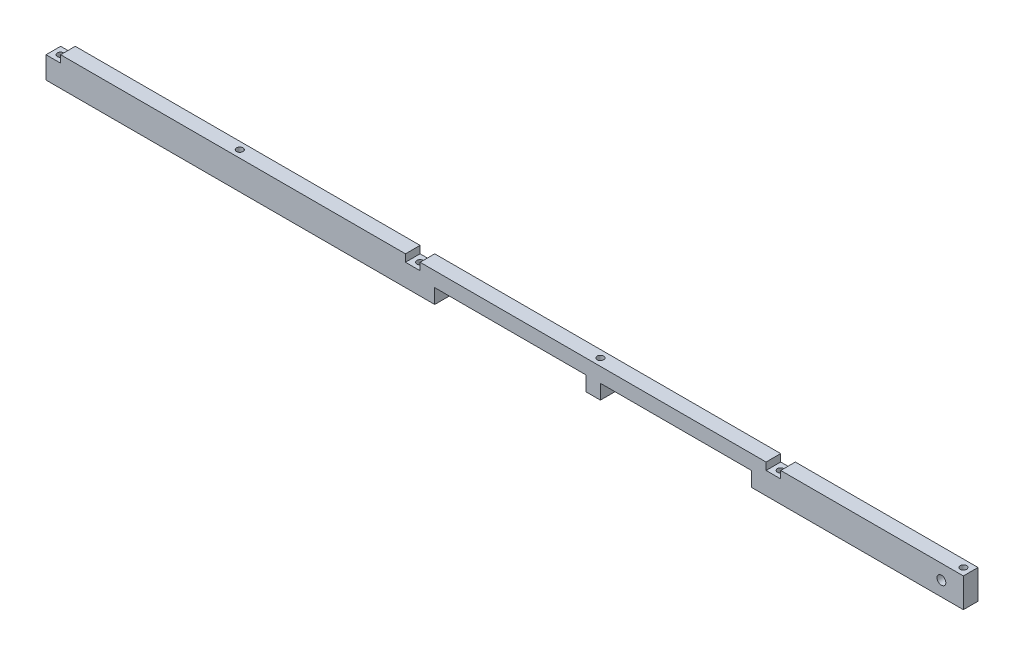
SolidWorks part; units mm, degrees
ref_plane "Front Plane" through (0, 0, 0) normal (0, 0, 1) x (1, 0, 0)
ref_plane "Top Plane" through (0, 0, 0) normal (0, 1, 0) x (1, 0, 0)
ref_plane "Right Plane" through (0, 0, 0) normal (1, 0, 0) x (0, 0, -1)
sketch "Sketch1" plane through (0, 0, 0) normal (1, 0, 0) x (0, 0, -1)
  line L1 (0, 0) -> (6.35, 0)
  line L2 (0, 0) -> (0, 12.7)
  line L3 (0, 12.7) -> (6.35, 12.7)
  line L4 (6.35, 0) -> (6.35, 12.7)
  dimension "D1" = 6.35
  dimension "D2" = 12.7
extrude "Boss-Extrude1" add sketch "Sketch1" along normal blind 398.018
hole_wizard "#34 (0.111) Diameter Hole1" positions "Sketch4" profile "Sketch5" hole size "#34" standard "ANSI Inch" end condition through all
sketch "Sketch4" plane through (0, 12.7, 0) normal (0, 1, 0) x (1, 0, 0)
  line L0 (0, 3.175) -> (398.018, 3.175) construction
  line L1 (0, 6.35) -> (0, 0) construction
  line L2 (398.018, 6.35) -> (398.018, 0) construction
  point P9 (3.175, 3.175)
  point P11 (159.131, 3.175)
  point P13 (80.899, 3.175)
  point P15 (237.363, 3.175)
  point P17 (315.595, 3.175)
  point P19 (394.843, 3.175)
  dimension "D1" = 3.175
  dimension "D2" = 77.724
  dimension "D3" = 78.232
  dimension "D4" = 78.232
  dimension "D5" = 78.232
  dimension "D6" = 79.248
sketch "Sketch5" plane through (3.175, 12.7, -3.175) normal (1, 0, 0) x (0, 0, 1)
  line L0 (0, 0) -> (0, 12.7)
  line L1 (0, 12.7) -> (1.4097, 12.7)
  line L2 (1.4097, 12.7) -> (1.4097, 0)
  line L5 (1.4097, 0) -> (0, 0)
  line L11 (0, -6.35) -> (0, 107.95) construction
  dimension "Thru Hole Dia." = 2.8194
  dimension "Thru Hole Depth" = 12.7
sketch "Sketch6" plane through (0, 0, 0) normal (0, 0, 1) x (1, 0, 0)
  line L0 (1.7653, 6.35) -> (4.5847, 6.35) construction
  line L1 (1.7653, 12.7) -> (1.7653, 0) construction
  line L2 (4.5847, 0) -> (4.5847, 12.7) construction
  line L3 (4.5847, 6.35) -> (79.4893, 6.35) construction
  line L4 (79.4893, 12.7) -> (79.4893, 0) construction
  line L6 (82.3087, 0) -> (82.3087, 12.7) construction
  line L7 (82.3087, 6.35) -> (157.7213, 6.35) construction
  line L8 (157.7213, 12.7) -> (157.7213, 0) construction
  line L9 (157.7213, 6.35) -> (160.5407, 6.35) construction
  line L10 (160.5407, 0) -> (160.5407, 12.7) construction
  line L11 (160.5407, 6.35) -> (235.9533, 6.35) construction
  line L12 (235.9533, 12.7) -> (235.9533, 0) construction
  line L14 (238.7727, 0) -> (238.7727, 12.7) construction
  line L15 (238.7727, 6.35) -> (314.1853, 6.35) construction
  line L16 (314.1853, 12.7) -> (314.1853, 0) construction
  line L17 (314.1853, 6.35) -> (317.0047, 6.35) construction
  line L18 (317.0047, 0) -> (317.0047, 12.7) construction
  line L19 (317.0047, 6.35) -> (393.4333, 6.35) construction
  line L20 (393.4333, 12.7) -> (393.4333, 0) construction
  line L23 (3.175, 6.35) -> (3.175, 12.7) construction
  line L24 (398.018, 12.7) -> (0, 12.7) construction
  line L26 (80.899, 12.7) -> (159.131, 6.35) construction
  line L27 (159.131, 6.35) -> (159.131, 12.7) construction
  line L28 (159.131, 12.7) -> (237.363, 6.35) construction
  line L30 (237.363, 12.7) -> (315.595, 6.35) construction
  line L31 (315.595, 6.35) -> (315.595, 12.7) construction
  line L32 (315.595, 12.7) -> (394.843, 6.35) construction
  line L41 (312.42, 9.525) -> (318.77, 9.525)
  line L42 (312.42, 9.525) -> (312.42, 15.875)
  line L43 (312.42, 15.875) -> (318.77, 15.875)
  line L44 (318.77, 9.525) -> (318.77, 15.875)
  line L45 (312.42, 9.525) -> (318.77, 15.875) construction
  line L46 (312.42, 15.875) -> (318.77, 9.525) construction
  line L53 (155.956, 9.525) -> (162.306, 9.525)
  line L54 (155.956, 9.525) -> (155.956, 15.875)
  line L55 (155.956, 15.875) -> (162.306, 15.875)
  line L56 (162.306, 9.525) -> (162.306, 15.875)
  line L57 (155.956, 9.525) -> (162.306, 15.875) construction
  line L58 (155.956, 15.875) -> (162.306, 9.525) construction
  line L65 (0, 9.525) -> (6.35, 9.525)
  line L66 (0, 9.525) -> (0, 15.875)
  line L67 (0, 15.875) -> (6.35, 15.875)
  line L68 (6.35, 9.525) -> (6.35, 15.875)
  line L69 (0, 9.525) -> (6.35, 15.875) construction
  line L70 (0, 15.875) -> (6.35, 9.525) construction
  dimension "D1" = 6.35
  dimension "D3" = 6.35
  dimension "D5" = 6.35
  dimension "D7" = 6.35
  dimension "D9" = 6.35
  dimension "D10" = 6.35
extrude "Cut-Extrude1" cut sketch "Sketch6" against normal through all
hole_wizard "Tap Drill for #10-24 Tap1" positions "Sketch8" profile "Sketch7" hole size "#10-24" standard "ANSI Inch" end condition through all
sketch "Sketch8" plane through (0, 0, 0) normal (0, 0, 1) x (1, 0, 0)
  line L0 (398.018, 6.35) -> (388.493, 6.35) construction
  line L1 (398.018, 12.7) -> (398.018, 0) construction
  point P2 (388.493, 6.35)
sketch "Sketch7" plane through (388.493, 6.35, 0) normal (1, 0, 0) x (0, -1, 0)
  line L0 (0, 0) -> (0, 6.35)
  line L1 (0, 6.35) -> (1.8986, 6.35)
  line L2 (1.8986, 6.35) -> (1.8986, 0)
  line L5 (1.8986, 0) -> (0, 0)
  line L11 (0, -6.35) -> (0, 107.95) construction
  dimension "Thru Hole Dia." = 3.7973
  dimension "Thru Hole Depth" = 6.35
sketch "Sketch9" plane through (0, 0, 0) normal (0, 0, 1) x (1, 0, 0)
  line L0 (398.018, 0) -> (0, 0) construction
  line L1 (306.07, 0) -> (240.538, 0)
  line L2 (306.07, 0) -> (306.07, 6.35)
  line L3 (306.07, 6.35) -> (240.538, 6.35)
  line L4 (240.538, 0) -> (240.538, 6.35)
  line L5 (312.42, 12.7) -> (312.42, 9.525) construction
  line L6 (234.188, 0) -> (168.656, 0)
  line L7 (234.188, 0) -> (234.188, 6.35)
  line L8 (234.188, 6.35) -> (168.656, 6.35)
  line L9 (168.656, 0) -> (168.656, 6.35)
  line L10 (162.306, 9.525) -> (162.306, 12.7) construction
  line L11 (238.7727, 0) -> (235.9533, 0)
  line L12 (238.7727, 0) -> (238.7727, 12.7) construction
  line L13 (235.9533, 12.7) -> (235.9533, 0) construction
  line L14 (240.538, 0) -> (234.188, 0)
  line L15 (238.7727, 6.35) -> (235.9533, 6.35)
  line L16 (168.656, 0) -> (234.188, 0)
  line L17 (240.538, 0) -> (306.07, 0)
  point P22 (237.363, 6.35)
  point P23 (237.363, 0)
  line M6 (0, 0) -> (398.018, 0)
  dimension "D1" = 6.35
  dimension "D2" = 6.35
  dimension "D3" = 6.35
  dimension "D4" = 6.35
  dimension "D5" = 6.35
extrude "Cut-Extrude3" cut sketch "Sketch9" against normal through all contours L9 L7 L8 M6 | L4 L2 L3 M6
